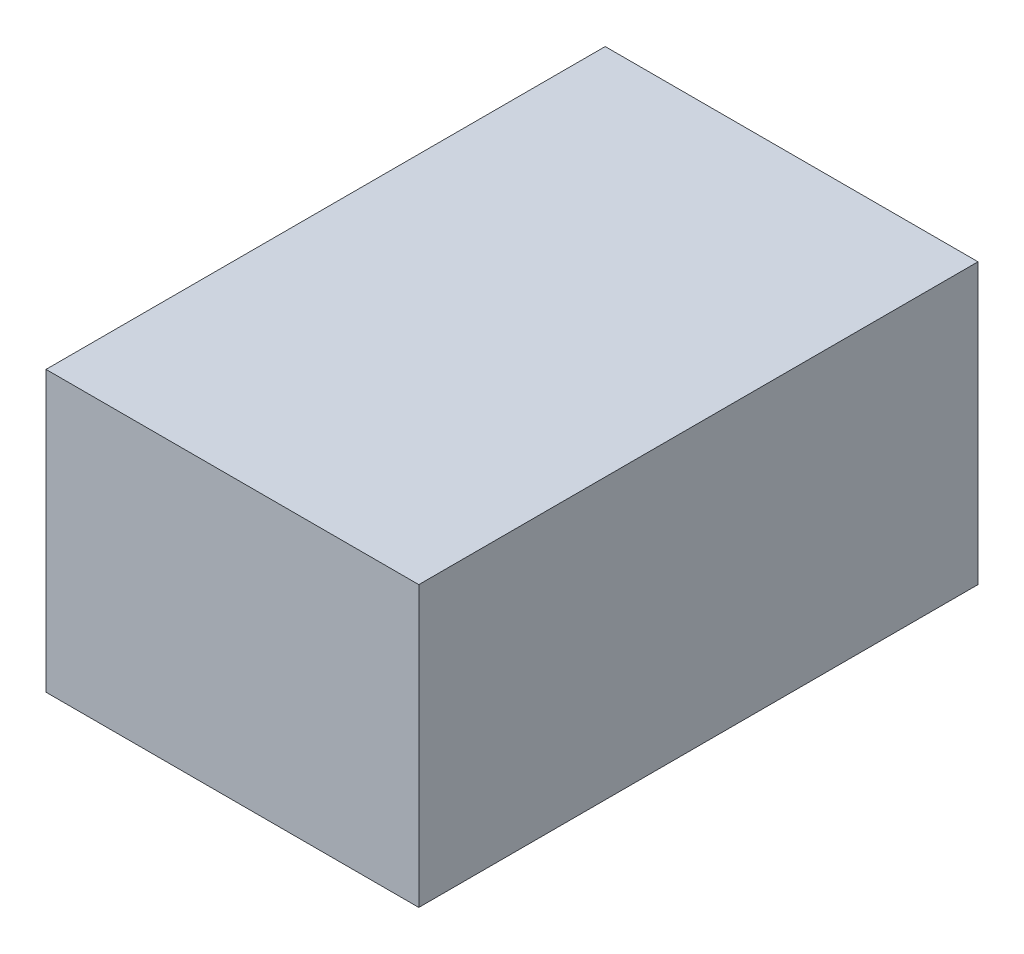
SolidWorks part; units mm, degrees
ref_plane "Front Plane" through (0, 0, 0) normal (0, 0, 1) x (1, 0, 0)
ref_plane "Top Plane" through (0, 0, 0) normal (0, 1, 0) x (1, 0, 0)
ref_plane "Right Plane" through (0, 0, 0) normal (1, 0, 0) x (0, 0, -1)
sketch "Sketch1" plane through (0, 0, 0) normal (0, 0, 1) x (1, 0, 0)
  line L1 (0, 0) -> (101.6, 0)
  line L2 (0, 0) -> (0, 76.2)
  line L3 (0, 76.2) -> (101.6, 76.2)
  line L4 (101.6, 0) -> (101.6, 76.2)
  dimension "D1" = 76.2
  dimension "D2" = 101.6
extrude "Boss-Extrude1" add sketch "Sketch1" along normal blind 152.4
